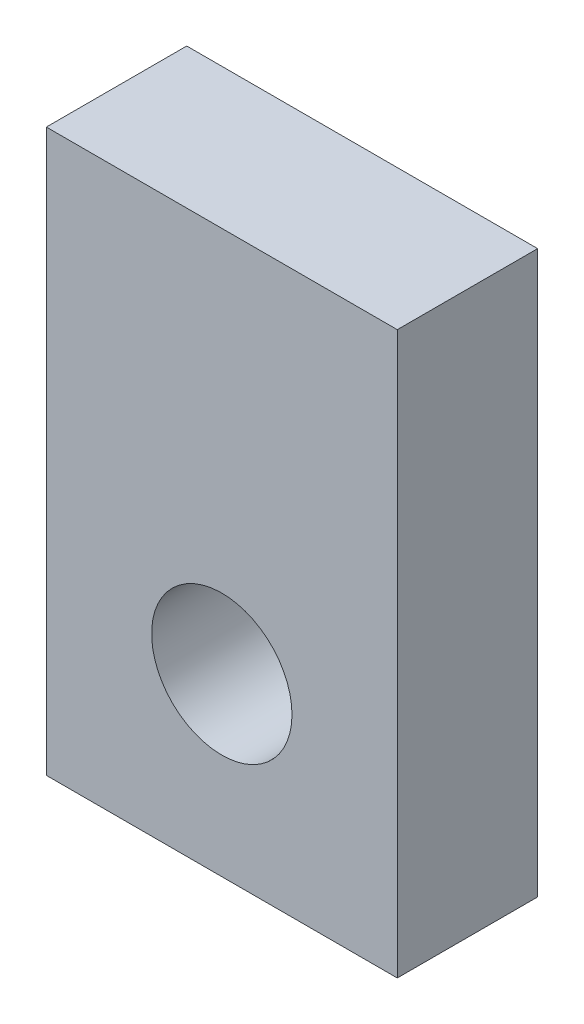
SolidWorks part; units mm, degrees
ref_plane "Front Plane" through (0, 0, 0) normal (0, 0, 1) x (1, 0, 0)
ref_plane "Top Plane" through (0, 0, 0) normal (0, 1, 0) x (1, 0, 0)
ref_plane "Right Plane" through (0, 0, 0) normal (1, 0, 0) x (0, 0, -1)
sketch "Sketch1" plane through (0, 0, 0) normal (0, 1, 0) x (1, 0, 0)
  line L1 (0, 0) -> (-10, 0)
  line L2 (0, 0) -> (0, 4)
  line L3 (0, 4) -> (-10, 4)
  line L4 (-10, 0) -> (-10, 4)
  dimension "D1" = 10
  dimension "D2" = 4
extrude "Boss-Extrude1" add sketch "Sketch1" along normal blind 16
sketch "Sketch2" plane through (0, 0, 0) normal (0, 0, 1) x (1, 0, 0)
  line L0 (-10, 16) -> (0, 16) construction
  circle A0 centre (-5, 5) radius 2
  point P6 (-5, 16)
  dimension "D1" = 4
  dimension "D2" = 5
extrude "Cut-Extrude1" cut sketch "Sketch2" against normal through all
